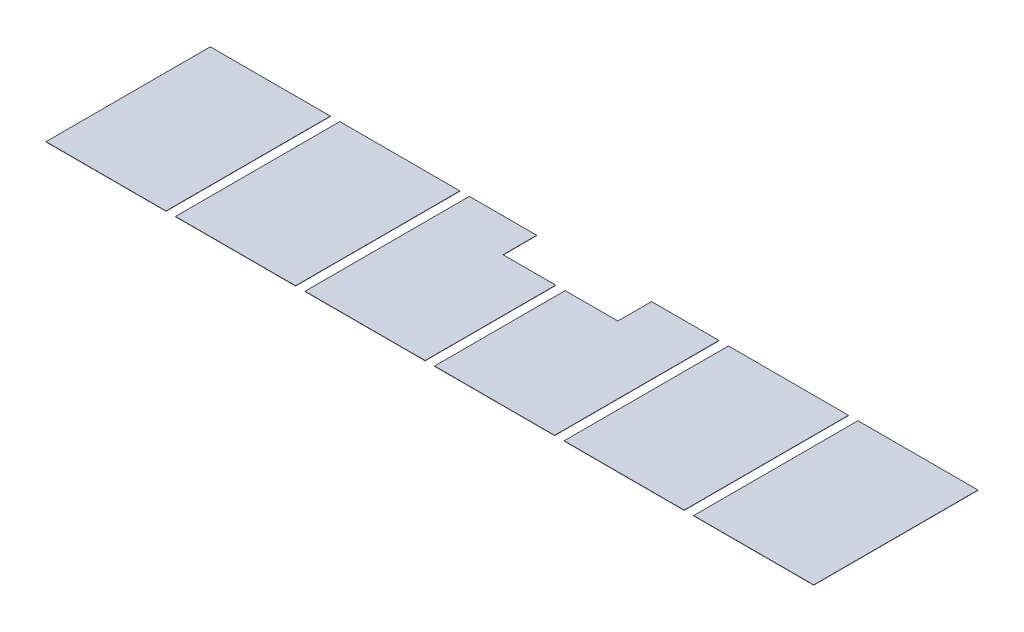
SolidWorks part; units mm, degrees
ref_plane "Front Plane" through (0, 0, 0) normal (0, 0, 1) x (1, 0, 0)
ref_plane "Top Plane" through (0, 0, 0) normal (0, 1, 0) x (1, 0, 0)
ref_plane "Right Plane" through (0, 0, 0) normal (1, 0, 0) x (0, 0, -1)
ref_plane "Insulated Subfloor Plane" through (0, 40.64, 0) normal (0, 1, 0) x (1, 0, 0)
sketch "Sketch1" plane through (0, 40.64, 0) normal (0, 1, 0) x (1, 0, 0)
  line L4 (3073.4, 2044.7) -> (1625.6, 2044.7)
  line L5 (1625.6, 2044.7) -> (1625.6, 63.5)
  line L6 (1625.6, 63.5) -> (3073.4, 63.5)
  line L7 (3073.4, 63.5) -> (3073.4, 2044.7)
  line L8 (3073.4, 2044.7) -> (1625.6, 2044.7)
  line L9 (1625.6, 2044.7) -> (1625.6, 63.5)
  line L10 (1625.6, 63.5) -> (3073.4, 63.5)
  line L11 (3073.4, 63.5) -> (3073.4, 2044.7)
  line L12 (1511.3, 2044.7) -> (63.5, 2044.7)
  line L13 (63.5, 2044.7) -> (63.5, 63.5)
  line L14 (63.5, 63.5) -> (1511.3, 63.5)
  line L15 (1511.3, 63.5) -> (1511.3, 2044.7)
  line L16 (1511.3, 2044.7) -> (63.5, 2044.7)
  line L17 (63.5, 2044.7) -> (63.5, 63.5)
  line L18 (63.5, 63.5) -> (1511.3, 63.5)
  line L19 (1511.3, 63.5) -> (1511.3, 2044.7)
  line L20 (9321.8, 2044.7) -> (7874, 2044.7)
  line L21 (7874, 2044.7) -> (7874, 63.5)
  line L22 (7874, 63.5) -> (9321.8, 63.5)
  line L23 (9321.8, 63.5) -> (9321.8, 2044.7)
  line L24 (9321.8, 2044.7) -> (7874, 2044.7)
  line L25 (7874, 2044.7) -> (7874, 63.5)
  line L26 (7874, 63.5) -> (9321.8, 63.5)
  line L27 (9321.8, 63.5) -> (9321.8, 2044.7)
  line L28 (7759.7, 63.5) -> (7759.7, 2044.7)
  line L29 (6311.9, 63.5) -> (7759.7, 63.5)
  line L30 (6311.9, 2044.7) -> (6311.9, 63.5)
  line L31 (7759.7, 2044.7) -> (6311.9, 2044.7)
  line L32 (7759.7, 63.5) -> (7759.7, 2044.7)
  line L33 (6311.9, 63.5) -> (7759.7, 63.5)
  line L34 (6311.9, 2044.7) -> (6311.9, 63.5)
  line L35 (7759.7, 2044.7) -> (6311.9, 2044.7)
  line L38 (6197.6, 2044.7) -> (5384.8, 2044.7)
  line L39 (6197.6, 63.5) -> (6197.6, 2044.7)
  line L40 (4749.8, 63.5) -> (6197.6, 63.5)
  line L41 (4749.8, 1638.3) -> (4749.8, 63.5)
  line L42 (5384.8, 1638.3) -> (4749.8, 1638.3)
  line L43 (5384.8, 2044.7) -> (5384.8, 1638.3)
  line L44 (6197.6, 2044.7) -> (5384.8, 2044.7)
  line L45 (6197.6, 63.5) -> (6197.6, 2044.7)
  line L46 (4749.8, 63.5) -> (6197.6, 63.5)
  line L47 (4749.8, 1638.3) -> (4749.8, 63.5)
  line L48 (5384.8, 1638.3) -> (4749.8, 1638.3)
  line L49 (5384.8, 2044.7) -> (5384.8, 1638.3)
  line L50 (3187.7, 2044.7) -> (3187.7, 63.5)
  line L51 (4000.5, 2044.7) -> (3187.7, 2044.7)
  line L52 (4000.5, 1638.3) -> (4000.5, 2044.7)
  line L53 (4635.5, 1638.3) -> (4000.5, 1638.3)
  line L54 (4635.5, 63.5) -> (4635.5, 1638.3)
  line L55 (3187.7, 63.5) -> (4635.5, 63.5)
  line L56 (3187.7, 2044.7) -> (3187.7, 63.5)
  line L57 (4000.5, 2044.7) -> (3187.7, 2044.7)
  line L58 (4000.5, 1638.3) -> (4000.5, 2044.7)
  line L59 (4635.5, 1638.3) -> (4000.5, 1638.3)
  line L60 (4635.5, 63.5) -> (4635.5, 1638.3)
  line L61 (3187.7, 63.5) -> (4635.5, 63.5)
  dimension "D1" = 0
  dimension "D2" = 0
  dimension "D3" = 0
  dimension "D4" = 0
  dimension "D5" = 0
  dimension "D6" = 0
extrude "Boss-Extrude3" add sketch "Sketch1" along normal up to surface (3.175 mm away)
